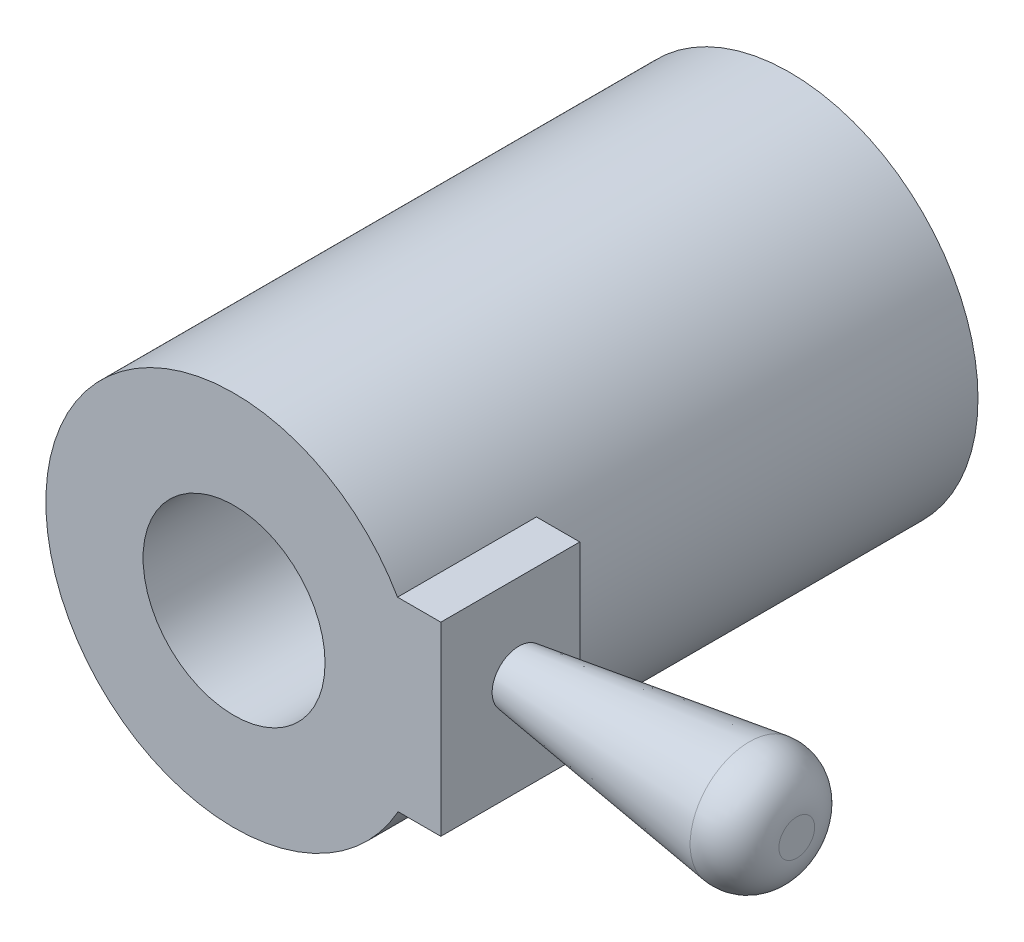
SolidWorks part; units mm, degrees
ref_plane "Front Plane" through (0, 0, 0) normal (0, 0, 1) x (1, 0, 0)
ref_plane "Top Plane" through (0, 0, 0) normal (0, 1, 0) x (1, 0, 0)
ref_plane "Right Plane" through (0, 0, 0) normal (1, 0, 0) x (0, 0, -1)
sketch "Sketch2" plane through (0, 0, 0) normal (0, 0, 1) x (1, 0, 0)
  circle A0 centre (0, 0) radius 16.637
  circle A1 centre (0, 0) radius 34.4106
  dimension "D1" = 33.274
extrude "Boss-Extrude1" add sketch "Sketch2" along normal blind 101.6
sketch "Sketch3" plane through (0, 0, 101.6) normal (0, 0, 1) x (1, 0, 0)
  line L1 (21.6442, 17.056) -> (37.8025, 17.056)
  line L2 (21.6442, 17.056) -> (21.6442, -16.8565)
  line L3 (21.6442, -16.8565) -> (37.8025, -16.8565)
  line L4 (37.8025, 17.056) -> (37.8025, -16.8565)
extrude "Boss-Extrude2" add sketch "Sketch3" against normal blind 25.4
sketch "Sketch4" plane through (37.8025, 0, 0) normal (1, 0, 0) x (0, 0, -1)
  circle A0 centre (-87.3249, 1.2266) radius 4.8963
extrude "Boss-Extrude3" add sketch "Sketch4" along normal blind 50.8 draft 8 draft outward yes
fillet "Fillet1" radius 7.62 1 edges at (88.6025, 1.2266, 75.2891)
